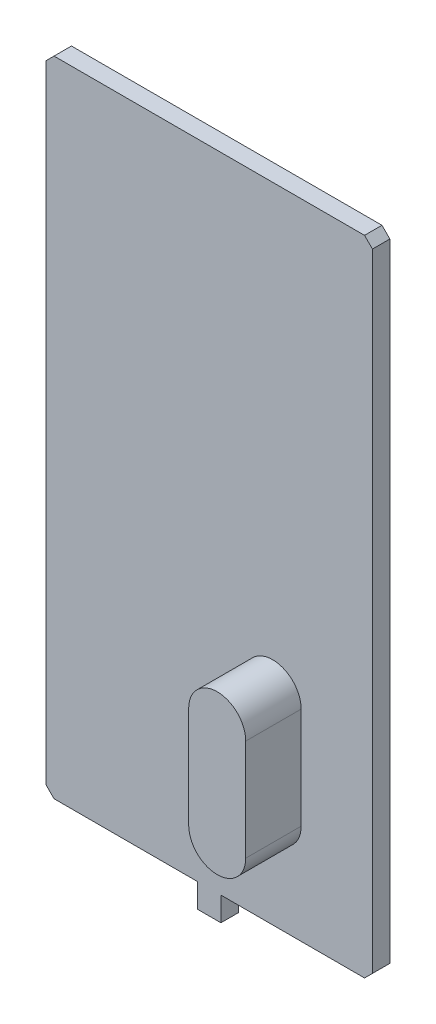
SolidWorks part; units mm, degrees
ref_plane "Спереди" through (0, 0, 0) normal (0, 0, 1) x (1, 0, 0)
ref_plane "Сверху" through (0, 0, 0) normal (0, 1, 0) x (1, 0, 0)
ref_plane "Справа" through (0, 0, 0) normal (1, 0, 0) x (0, 0, -1)
sketch "Эскиз1" plane through (0, 0, 0) normal (0, 0, 1) x (1, 0, 0)
  line L1 (-10.3, 20.3) -> (10.3, 20.3)
  line L2 (-10.3, 20.3) -> (-10.3, -20.3)
  line L3 (-10.3, -20.3) -> (10.3, -20.3)
  line L4 (10.3, 20.3) -> (10.3, -20.3)
  line L5 (-10.3, 20.3) -> (10.3, -20.3) construction
  line L6 (-10.3, -20.3) -> (10.3, 20.3) construction
  point P0 (0, 0)
  dimension "D1" = 20.6
  dimension "D2" = 40.6
extrude "Бобышка-Вытянуть1" add sketch "Эскиз1" along normal blind 1.1
sketch "Эскиз2" plane through (0, 0, 1.1) normal (0, 0, 1) x (1, 0, 0)
  line L0 (4, -7.6) -> (4, -14) construction
  line L1 (5.8, -7.6) -> (5.8, -14)
  line L2 (2.2, -7.6) -> (2.2, -14)
  line L3 (5.8, 20.3) -> (5.8, -20.3) construction
  line L4 (10.3, 20.3) -> (-10.3, 20.3) construction
  line L5 (-10.3, -20.3) -> (10.3, -20.3) construction
  line L6 (10.3, -20.3) -> (10.3, 20.3) construction
  line L7 (-10.3, -15.8) -> (10.3, -15.8) construction
  line L8 (-10.3, 20.3) -> (-10.3, -20.3) construction
  arc A0 (5.8, -7.6) -> (2.2, -7.6) centre (4, -7.6) ccw
  arc A1 (2.2, -14) -> (5.8, -14) centre (4, -14) ccw
  point P2 (4, -10.8)
  dimension "D1" = 1.8
  dimension "D2" = 6.4
  dimension "D3" = 4.5
  dimension "D4" = 4.5
extrude "Бобышка-Вытянуть2" add sketch "Эскиз2" along normal blind 3.5
sketch "Эскиз3" plane through (0, 0, 1.1) normal (0, 0, 1) x (1, 0, 0)
  line L0 (0, -20.3) -> (0, -18.3391) construction
  line L1 (-10.3, -20.3) -> (10.3, -20.3) construction
  line L3 (-0.7346, -18.7849) -> (0.7346, -18.7849)
  line L4 (-0.7346, -18.7849) -> (-0.7346, -21.8151)
  line L5 (-0.7346, -21.8151) -> (0.7346, -21.8151)
  line L6 (0.7346, -18.7849) -> (0.7346, -21.8151)
  line L7 (-0.7346, -18.7849) -> (0.7346, -21.8151) construction
  line L8 (-0.7346, -21.8151) -> (0.7346, -18.7849) construction
extrude "Бобышка-Вытянуть3" add sketch "Эскиз3" against normal up to surface (1.1 mm away) up to face at (0, 0, 0)
chamfer "Фаска1" distance 0.5 angle 45 4 edges at (-10.3, -20.3, 0.55) (10.3, -20.3, 0.55) (10.3, 20.3, 0.55) (-10.3, 20.3, 0.55)
